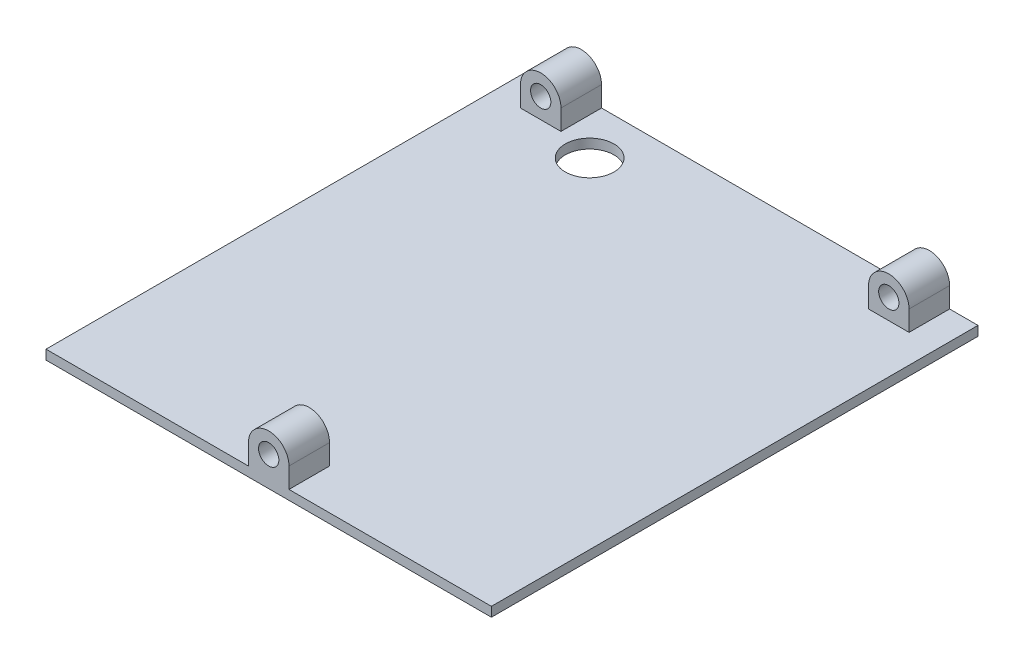
SolidWorks part; units mm, degrees
ref_plane "Front Plane" through (0, 0, 0) normal (0, 0, 1) x (1, 0, 0)
ref_plane "Top Plane" through (0, 0, 0) normal (0, 1, 0) x (1, 0, 0)
ref_plane "Right Plane" through (0, 0, 0) normal (1, 0, 0) x (0, 0, -1)
sketch "Sketch1" plane through (0, 0, 0) normal (0, 1, 0) x (1, 0, 0)
  line L1 (0, 0) -> (139.5, 0)
  line L2 (0, 0) -> (0, 152.4)
  line L3 (0, 152.4) -> (139.5, 152.4)
  line L4 (139.5, 0) -> (139.5, 152.4)
  dimension "D1" = 152.4
  dimension "D2" = 139.5
extrude "Boss-Extrude1" add sketch "Sketch1" along normal blind 6.35
sketch "Sketch2" plane through (0, 6.35, 0) normal (0, 1, 0) x (1, 0, 0)
  line L0 (0, 0) -> (139.5, 0) construction
  line L1 (0, 152.4) -> (139.5, 152.4)
  line L2 (0, 152.4) -> (0, 0)
  line L3 (0, 0) -> (139.5, 0)
  line L4 (139.5, 152.4) -> (139.5, 0)
  line L5 (139.5, 0) -> (139.5, 152.4) construction
extrude "Cut-Extrude1" cut sketch "Sketch2" against normal blind 3.375
sketch "Sketch3" plane through (0, 0, 0) normal (0, 0, 1) x (1, 0, 0)
  line L0 (63.4, 9.325) -> (63.4, 2.975)
  line L1 (63.4, 2.975) -> (76.1, 2.975)
  line L2 (76.1, 9.325) -> (76.1, 2.975)
  line L3 (0, 2.975) -> (139.5, 2.975) construction
  line L4 (139.5, 2.975) -> (0, 2.975) construction
  arc A0 (76.1, 9.325) -> (63.4, 9.325) centre (69.75, 9.325) ccw
  circle A1 centre (69.75, 9.325) radius 3.175
  point P6 (69.75, 2.975)
  point P9 (69.75, 2.975)
  dimension "D1" = 6.35
  dimension "D2" = 12.7
  dimension "D8" = 6.35
  dimension "D5" = 6.35
extrude "Boss-Extrude2" add sketch "Sketch3" against normal blind 12.7
sketch "Sketch4" plane through (0, 0, -152.4) normal (0, 0, -1) x (-1, 0, 0)
  line L0 (-130.61, 9.325) -> (-130.61, 2.975)
  line L1 (-130.61, 2.975) -> (-117.91, 2.975)
  line L2 (-117.91, 9.325) -> (-117.91, 2.975)
  line L3 (-21.59, 9.325) -> (-21.59, 2.975)
  line L4 (-21.59, 2.975) -> (-8.89, 2.975)
  line L5 (-8.89, 9.325) -> (-8.89, 2.975)
  line L6 (-139.5, 2.975) -> (0, 2.975) construction
  line L7 (0, 2.975) -> (0, 0) construction
  line L8 (-139.5, 2.975) -> (-139.5, 0) construction
  arc A0 (-117.91, 9.325) -> (-130.61, 9.325) centre (-124.26, 9.325) ccw
  circle A1 centre (-124.26, 9.325) radius 3.175
  arc A2 (-8.89, 9.325) -> (-21.59, 9.325) centre (-15.24, 9.325) ccw
  circle A3 centre (-15.24, 9.325) radius 3.175
  dimension "D1" = 6.35
  dimension "D3" = 6.35
  dimension "D5" = 6.35
  dimension "D7" = 6.35
  dimension "D2" = 6.35
  dimension "D4" = 12.7
  dimension "D6" = 6.35
  dimension "D8" = 12.7
  dimension "D9" = 8.89
  dimension "D10" = 8.89
  dimension "D11" = 15.24
  dimension "D12" = 15.24
extrude "Boss-Extrude3" add sketch "Sketch4" against normal blind 12.7
sketch "Sketch5" plane through (0, 0, 0) normal (0, -1, 0) x (1, 0, 0)
  line L0 (0, -152.4) -> (0, 0) construction
  line L1 (139.5, -152.4) -> (0, -152.4) construction
  circle A0 centre (33.274, -136.9916) radius 7.62
  dimension "D1" = 15.24
  dimension "D2" = 33.274
  dimension "D3" = 15.4084
extrude "Cut-Extrude2" cut sketch "Sketch5" against normal through all
